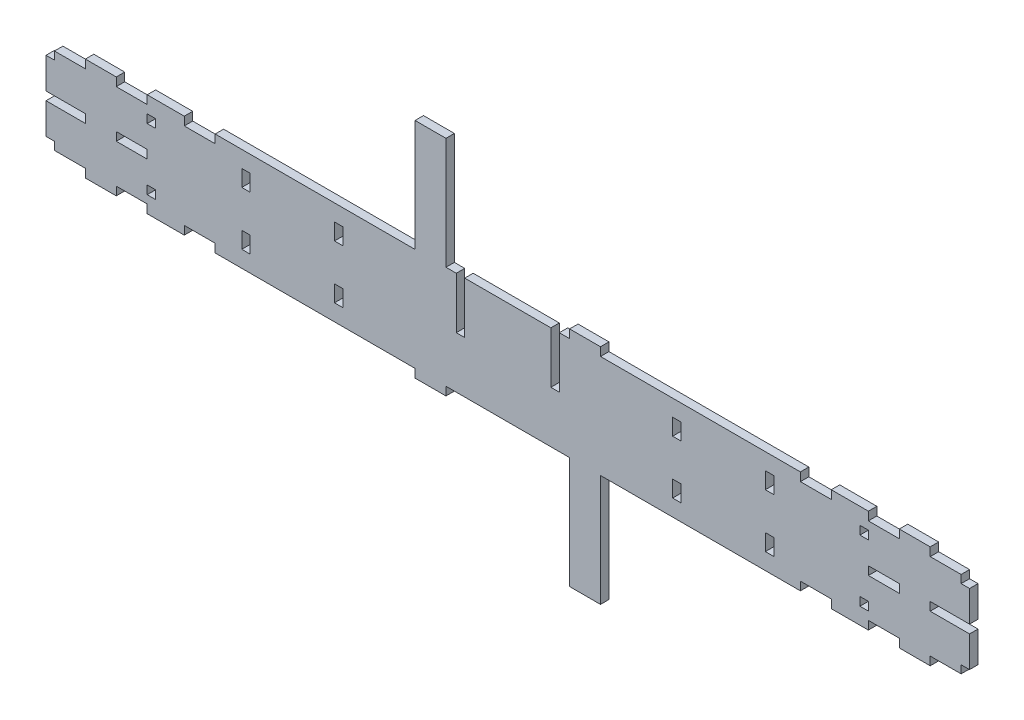
SolidWorks part; units mm, degrees
material "Corrugated Paper"
ref_plane "Front Plane" through (0, 0, 0) normal (0, 0, 1) x (1, 0, 0)
ref_plane "Top Plane" through (0, 0, 0) normal (0, 1, 0) x (1, 0, 0)
ref_plane "Right Plane" through (0, 0, 0) normal (1, 0, 0) x (0, 0, -1)
sketch "Sketch1" plane through (0, 0, 0) normal (0, 0, 1) x (1, 0, 0)
  line L0 (-220, 0) -> (220, 0) construction
  line L1 (-220, -25) -> (220, -25)
  line L2 (-220, -25) -> (-220, 25)
  line L3 (-220, 25) -> (220, 25)
  line L4 (220, -25) -> (220, 25)
  line L5 (-220, -25) -> (220, 25) construction
  line L6 (-220, 25) -> (220, -25) construction
  line L7 (-220, 17.05) -> (-224.1, 17.05)
  line L8 (-220, 17.05) -> (-220, 2.05)
  line L9 (-220, 2.05) -> (-224.1, 2.05)
  line L10 (-224.1, 17.05) -> (-224.1, 2.05)
  line L11 (-220, 25) -> (-205, 25)
  line L12 (-220, 25) -> (-220, 20.9)
  line L13 (-220, 20.9) -> (-205, 20.9)
  line L14 (-205, 25) -> (-205, 20.9)
  line L15 (-30, 25) -> (-45, 25)
  line L16 (-30, 25) -> (-30, 79.2)
  line L17 (-30, 79.2) -> (-45, 79.2)
  line L18 (-45, 25) -> (-45, 79.2)
  line L19 (-20.9, 25) -> (-25, 25)
  line L20 (-20.9, 25) -> (-20.9, 0)
  line L21 (-20.9, 0) -> (-25, 0)
  line L22 (-25, 25) -> (-25, 0)
  line L23 (-84.1, 17) -> (-80, 17)
  line L24 (-84.1, 17) -> (-84.1, 9)
  line L25 (-84.1, 9) -> (-80, 9)
  line L26 (-80, 17) -> (-80, 9)
  line L27 (-129.1, 17) -> (-125, 17)
  line L28 (-129.1, 17) -> (-129.1, 9)
  line L29 (-129.1, 9) -> (-125, 9)
  line L30 (-125, 17) -> (-125, 9)
  line L31 (-190, 25) -> (-175, 25)
  line L32 (-190, 25) -> (-190, 20.9)
  line L33 (-190, 20.9) -> (-175, 20.9)
  line L34 (-175, 25) -> (-175, 20.9)
  line L35 (0, 25) -> (0, -25) construction
  line L36 (-205, 25) -> (-190, 25) construction
  line L37 (-220, 2.05) -> (-205, 2.05)
  line L38 (-220, 2.05) -> (-220, -2.05)
  line L39 (-220, -2.05) -> (-205, -2.05)
  line L40 (-205, 2.05) -> (-205, -2.05)
  line L41 (-190, 2.05) -> (-175, 2.05)
  line L42 (-190, 2.05) -> (-190, -2.05)
  line L43 (-190, -2.05) -> (-175, -2.05)
  line L44 (-175, 2.05) -> (-175, -2.05)
  line L45 (205, 25) -> (190, 25) construction
  line L46 (175, 2.05) -> (175, -2.05)
  line L47 (190, -2.05) -> (175, -2.05)
  line L48 (190, 2.05) -> (190, -2.05)
  line L49 (190, 2.05) -> (175, 2.05)
  line L50 (205, 2.05) -> (205, -2.05)
  line L51 (220, -2.05) -> (205, -2.05)
  line L52 (220, 2.05) -> (220, -2.05)
  line L53 (220, 2.05) -> (205, 2.05)
  line L54 (175, 25) -> (175, 20.9)
  line L55 (190, 20.9) -> (175, 20.9)
  line L56 (190, 25) -> (190, 20.9)
  line L57 (190, 25) -> (175, 25)
  line L58 (125, 17) -> (125, 9)
  line L59 (129.1, 9) -> (125, 9)
  line L60 (129.1, 17) -> (129.1, 9)
  line L61 (129.1, 17) -> (125, 17)
  line L62 (80, 17) -> (80, 9)
  line L63 (84.1, 9) -> (80, 9)
  line L64 (84.1, 17) -> (84.1, 9)
  line L65 (84.1, 17) -> (80, 17)
  line L66 (25, 25) -> (25, 0)
  line L67 (20.9, 0) -> (25, 0)
  line L68 (20.9, 25) -> (20.9, 0)
  line L69 (20.9, 25) -> (25, 25)
  line L70 (45, 25) -> (45, 79.2)
  line L71 (30, 79.2) -> (45, 79.2)
  line L72 (30, 25) -> (30, 79.2)
  line L73 (30, 25) -> (45, 25)
  line L74 (205, 25) -> (205, 20.9)
  line L75 (220, 20.9) -> (205, 20.9)
  line L76 (220, 25) -> (220, 20.9)
  line L77 (220, 25) -> (205, 25)
  line L78 (224.1, 17.05) -> (224.1, 2.05)
  line L79 (220, 2.05) -> (224.1, 2.05)
  line L80 (220, 17.05) -> (220, 2.05)
  line L81 (220, 17.05) -> (224.1, 17.05)
  line L82 (205, -25) -> (190, -25) construction
  line L83 (-205, -25) -> (-190, -25) construction
  line L84 (220, -17.05) -> (224.1, -17.05)
  line L85 (220, -17.05) -> (220, -2.05)
  line L86 (220, -2.05) -> (224.1, -2.05)
  line L87 (224.1, -17.05) -> (224.1, -2.05)
  line L88 (220, -25) -> (205, -25)
  line L89 (220, -25) -> (220, -20.9)
  line L90 (220, -20.9) -> (205, -20.9)
  line L91 (205, -25) -> (205, -20.9)
  line L92 (30, -25) -> (45, -25)
  line L93 (30, -25) -> (30, -79.2)
  line L94 (30, -79.2) -> (45, -79.2)
  line L95 (45, -25) -> (45, -79.2)
  line L96 (20.9, -25) -> (25, -25)
  line L97 (84.1, -17) -> (80, -17)
  line L98 (84.1, -17) -> (84.1, -9)
  line L99 (84.1, -9) -> (80, -9)
  line L100 (80, -17) -> (80, -9)
  line L101 (129.1, -17) -> (125, -17)
  line L102 (129.1, -17) -> (129.1, -9)
  line L103 (129.1, -9) -> (125, -9)
  line L104 (125, -17) -> (125, -9)
  line L105 (190, -25) -> (175, -25)
  line L106 (190, -25) -> (190, -20.9)
  line L107 (190, -20.9) -> (175, -20.9)
  line L108 (175, -25) -> (175, -20.9)
  line L109 (220, -2.05) -> (205, -2.05)
  line L110 (220, 2.05) -> (205, 2.05)
  line L111 (190, -2.05) -> (175, -2.05)
  line L112 (190, 2.05) -> (175, 2.05)
  line L113 (-190, 2.05) -> (-175, 2.05)
  line L114 (-190, -2.05) -> (-175, -2.05)
  line L115 (-220, 2.05) -> (-205, 2.05)
  line L116 (-220, -2.05) -> (-205, -2.05)
  line L117 (-175, -25) -> (-175, -20.9)
  line L118 (-190, -20.9) -> (-175, -20.9)
  line L119 (-190, -25) -> (-190, -20.9)
  line L120 (-190, -25) -> (-175, -25)
  line L121 (-125, -17) -> (-125, -9)
  line L122 (-129.1, -9) -> (-125, -9)
  line L123 (-129.1, -17) -> (-129.1, -9)
  line L124 (-129.1, -17) -> (-125, -17)
  line L125 (-80, -17) -> (-80, -9)
  line L126 (-84.1, -9) -> (-80, -9)
  line L127 (-84.1, -17) -> (-84.1, -9)
  line L128 (-84.1, -17) -> (-80, -17)
  line L129 (-20.9, -25) -> (-25, -25)
  line L130 (-45, -25) -> (-45, -79.2)
  line L131 (-30, -79.2) -> (-45, -79.2)
  line L132 (-30, -25) -> (-30, -79.2)
  line L133 (-30, -25) -> (-45, -25)
  line L134 (-205, -25) -> (-205, -20.9)
  line L135 (-220, -20.9) -> (-205, -20.9)
  line L136 (-220, -25) -> (-220, -20.9)
  line L137 (-220, -25) -> (-205, -25)
  line L138 (-224.1, -17.05) -> (-224.1, -2.05)
  line L139 (-220, -2.05) -> (-224.1, -2.05)
  line L140 (-220, -17.05) -> (-220, -2.05)
  line L141 (-220, -17.05) -> (-224.1, -17.05)
  line L142 (-220, -25) -> (220, -25)
  line L143 (-170.9, -17) -> (-170.9, -12.9)
  line L144 (-175, 17) -> (-170.9, 17)
  line L145 (-175, 17) -> (-175, 12.9)
  line L146 (-175, 12.9) -> (-170.9, 12.9)
  line L147 (-170.9, 17) -> (-170.9, 12.9)
  line L148 (-175, -12.9) -> (-170.9, -12.9)
  line L149 (-175, -17) -> (-175, -12.9)
  line L150 (-175, -17) -> (-170.9, -17)
  line L151 (175, -17) -> (170.9, -17)
  line L152 (175, -17) -> (175, -12.9)
  line L153 (175, -12.9) -> (170.9, -12.9)
  line L154 (170.9, 17) -> (170.9, 12.9)
  line L155 (175, 12.9) -> (170.9, 12.9)
  line L156 (175, 17) -> (175, 12.9)
  line L157 (175, 17) -> (170.9, 17)
  line L158 (170.9, -17) -> (170.9, -12.9)
  line L159 (142, 25) -> (142, 20.9)
  line L160 (-157, 25) -> (-142, 25)
  line L161 (-157, 25) -> (-157, 20.9)
  line L162 (-157, 20.9) -> (-142, 20.9)
  line L163 (-142, 25) -> (-142, 20.9)
  line L164 (157, 20.9) -> (142, 20.9)
  line L165 (157, 25) -> (157, 20.9)
  line L166 (157, 25) -> (142, 25)
  line L167 (-142, -25) -> (-142, -20.9)
  line L168 (-157, -20.9) -> (-142, -20.9)
  line L169 (-157, -25) -> (-157, -20.9)
  line L170 (-157, -25) -> (-142, -25)
  line L171 (157, -25) -> (142, -25)
  line L172 (157, -25) -> (157, -20.9)
  line L173 (157, -20.9) -> (142, -20.9)
  line L174 (142, -25) -> (142, -20.9)
  point P0 (0, 0)
  dimension "D1" = 15
  dimension "D2" = 440
  dimension "D3" = 54.2
  dimension "D4" = 50
  dimension "D5" = 8
  dimension "D6" = 25
  dimension "D7" = 30
  dimension "D8" = 80
  dimension "D9" = 125
  dimension "D10" = 4.1
  dimension "D11" = 8
  dimension "D12" = 18
  dimension "D13" = 4.1
extrude "Boss-Extrude1" add sketch "Sketch1" along normal blind 4.1 contours L2 L135 L134 L1 L119 L118 L117 L108 L107 L106 L91 L90 L4 L51 L50 L53 L75 L74 L3 L56 L55 L54 L66 L67 L68 L20 L21 L22 L34 L33 L32 | L18 L3 L16 L17 | L72 L3 L70 L71 | L132 L1 L130 L131 | L81 L4 L79 L78 | L84 L87 L86 L4 | L8 L7 L10 L9 | L140 L141 L138 L139 | L94 L95 L92 L93
sketch "Sketch2" plane through (0, 79.2, 0) normal (0, 1, 0) x (1, 0, 0)
  line L1 (30, 0) -> (45, 0)
  line L2 (30, 0) -> (30, -4.1)
  line L3 (30, -4.1) -> (45, -4.1)
  line L4 (45, 0) -> (45, -4.1)
extrude "top right" cut sketch "Sketch2" against normal blind 50.1
sketch "Sketch3" plane through (0, -79.2, 0) normal (0, -1, 0) x (1, 0, 0)
  line L1 (-30, 0) -> (-45, 0)
  line L2 (-30, 0) -> (-30, 4.1)
  line L3 (-30, 4.1) -> (-45, 4.1)
  line L4 (-45, 0) -> (-45, 4.1)
extrude "bottom left" cut sketch "Sketch3" against normal blind 50.1
sketch "Sketch4" [suppressed] plane through (0, 65.2, 0) normal (0, 1, 0) x (1, 0, 0)
  line L1 (-45, 0) -> (-30, 0)
  line L2 (-45, 0) -> (-45, -4.1)
  line L3 (-45, -4.1) -> (-30, -4.1)
  line L4 (-30, 0) -> (-30, -4.1)
extrude "top left" [suppressed] cut sketch "Sketch4" against normal blind 36.1
sketch "Sketch5" [suppressed] plane through (0, -65.2, 0) normal (0, -1, 0) x (1, 0, 0)
  line L1 (30, 4.1) -> (45, 4.1)
  line L2 (30, 4.1) -> (30, 0)
  line L3 (30, 0) -> (45, 0)
  line L4 (45, 4.1) -> (45, 0)
extrude "bottom right" [suppressed] cut sketch "Sketch5" against normal blind 36.1
